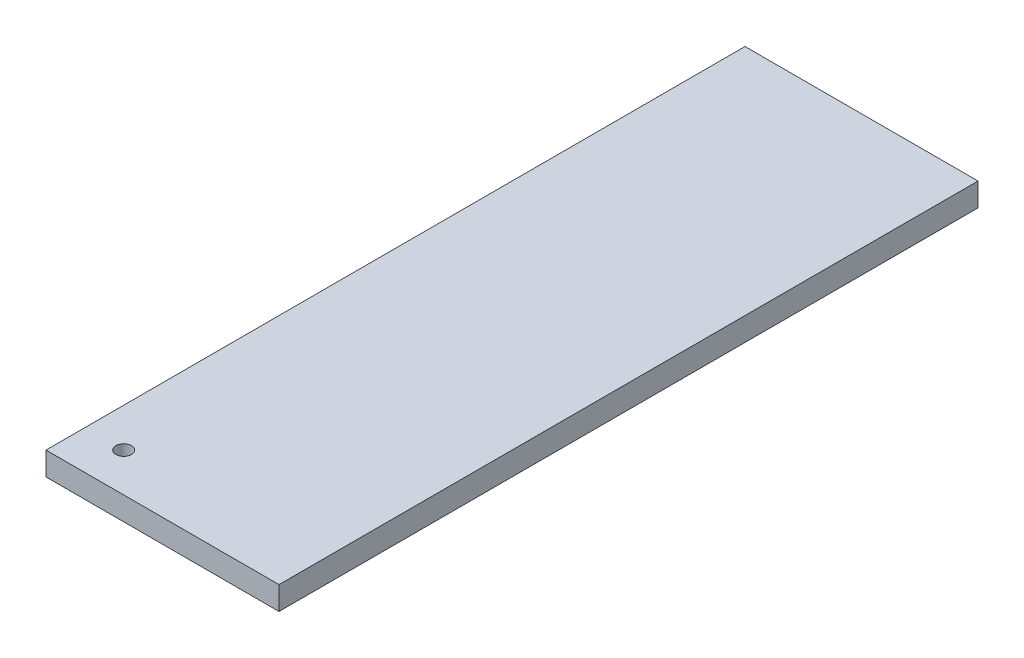
SolidWorks part; units mm, degrees
ref_plane "Front Plane" through (0, 0, 0) normal (0, 0, 1) x (1, 0, 0)
ref_plane "Top Plane" through (0, 0, 0) normal (0, 1, 0) x (1, 0, 0)
ref_plane "Right Plane" through (0, 0, 0) normal (1, 0, 0) x (0, 0, -1)
sketch "Sketch1" plane through (0, 0, 0) normal (0, 1, 0) x (1, 0, 0)
  line L1 (0, 0) -> (30, 0)
  line L2 (0, 0) -> (0, 90)
  line L3 (0, 90) -> (30, 90)
  line L4 (30, 0) -> (30, 90)
  circle A0 centre (5, 5) radius 1
  point P7 (0, 0)
  dimension "D3" = 2
  dimension "D4" = 5
  dimension "D5" = 5
  dimension "D1" = 30
  dimension "D2" = 90
extrude "Boss-Extrude1" add sketch "Sketch1" along normal blind 3
